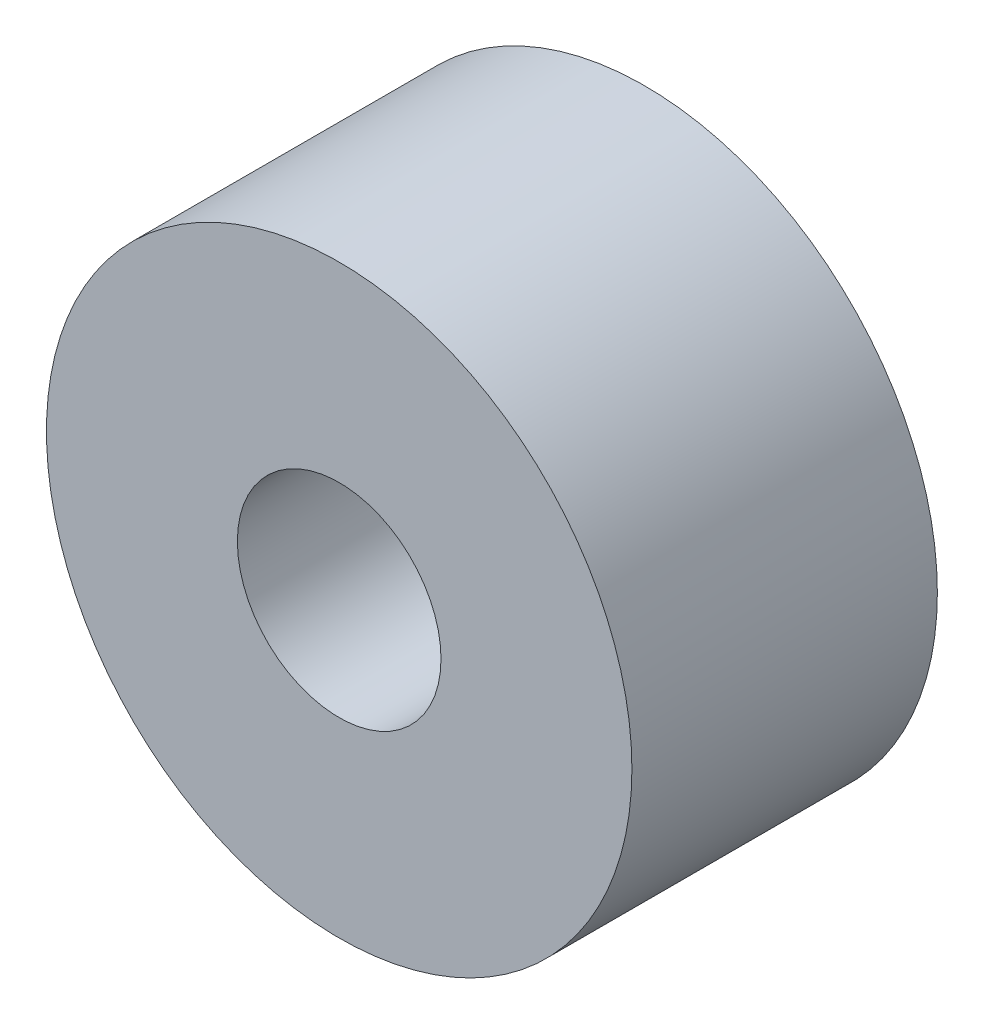
SolidWorks part; units mm, degrees
ref_plane "Front Plane" through (0, 0, 0) normal (0, 0, 1) x (1, 0, 0)
ref_plane "Top Plane" through (0, 0, 0) normal (0, 1, 0) x (1, 0, 0)
ref_plane "Right Plane" through (0, 0, 0) normal (1, 0, 0) x (0, 0, -1)
sketch "Sketch1" plane through (0, 0, 25.7668) normal (0, 0, 1) x (1, 0, 0)
  circle A0 centre (0, 0) radius 2
  circle A1 centre (0, 0) radius 5.75
  dimension "D1" = 4
  dimension "D2" = 11.5
extrude "Boss-Extrude1" add sketch "Sketch1" along normal blind 6
